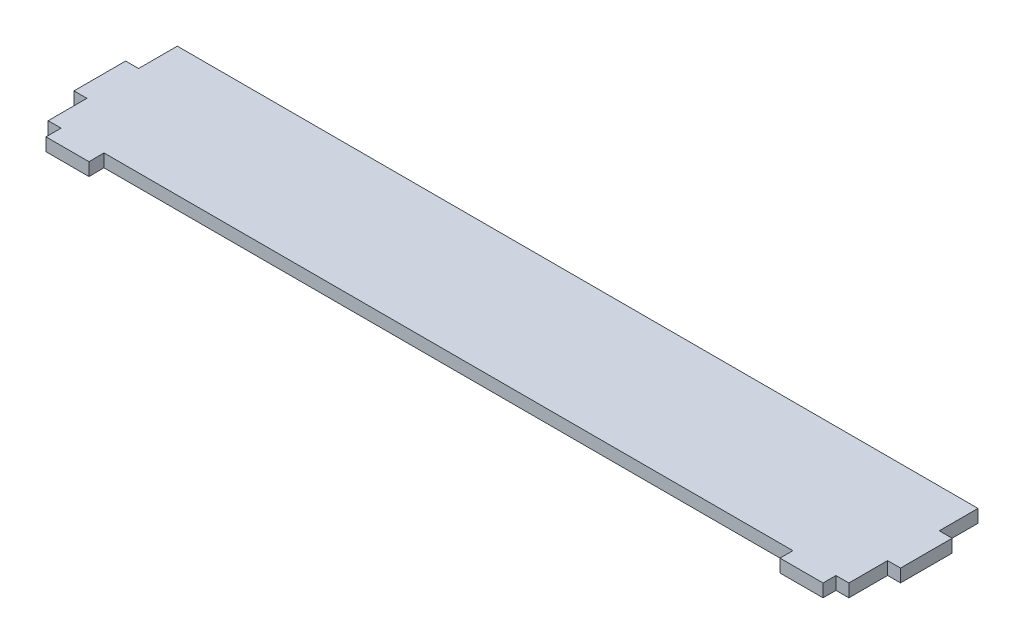
SolidWorks part; units mm, degrees
ref_plane "前视基准面" through (0, 0, 0) normal (0, 0, 1) x (1, 0, 0)
ref_plane "上视基准面" through (0, 0, 0) normal (0, 1, 0) x (1, 0, 0)
ref_plane "右视基准面" through (0, 0, 0) normal (1, 0, 0) x (0, 0, -1)
sketch "草图4" plane through (0, 0, 0) normal (0, 1, 0) x (1, 0, 0)
  line L0 (0, 0) -> (0.05, 0)
  line L1 (0, 0) -> (0.05, 0)
  line L3 (0, 30) -> (180, 30)
  line L5 (0, 0) -> (0, -3.5048)
  line L6 (0, 0) -> (0.05, 0)
  line L7 (10, 0) -> (9.95, 0)
  line L8 (0, -3.5048) -> (10, -3.5048)
  line L9 (10, -3.5048) -> (9.95, 0)
  line L10 (180, 0) -> (179.95, 0)
  line L11 (180, 0) -> (180, -3)
  line L12 (180, 0) -> (179.95, 0)
  line L13 (170, 0) -> (170.05, 0)
  line L14 (180, -3) -> (170, -3)
  line L15 (170, -3) -> (170, 0)
  line L24 (-3, 21) -> (-6, 21)
  line L25 (-6, 21) -> (-6, 9)
  line L26 (-6, 9) -> (-3, 9)
  line L27 (-3, 21) -> (-3, 30)
  line L28 (-3, 30) -> (0, 30)
  line L29 (-3, 9) -> (-3, 0)
  line L30 (-3, 0) -> (0, 0)
  line L31 (9.95, 0) -> (170.05, 0)
  line L32 (9.95, 0) -> (10, 0)
  line L33 (170.05, 0) -> (170, 0)
  line L34 (179.95, 0) -> (180, 0)
  line L35 (179.95, 0) -> (183, 0)
  line L36 (183, 0) -> (183, 9)
  line L37 (183, 21) -> (183, 30)
  line L38 (183, 30) -> (180, 30)
  line L39 (183, 21) -> (186, 21)
  line L40 (186, 21) -> (186, 9)
  line L41 (186, 9) -> (183, 9)
extrude "凸台-拉伸1" add sketch "草图4" along normal blind 3
